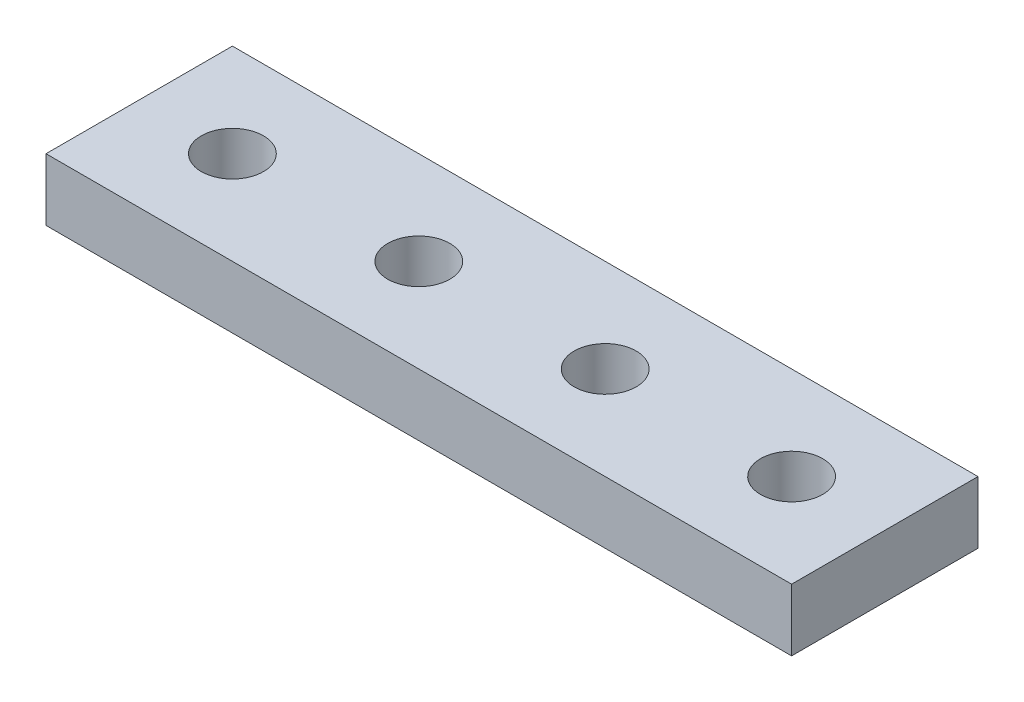
SolidWorks part; units mm, degrees
ref_plane "Front Plane" through (0, 0, 0) normal (0, 0, 1) x (1, 0, 0)
ref_plane "Top Plane" through (0, 0, 0) normal (0, 1, 0) x (1, 0, 0)
ref_plane "Right Plane" through (0, 0, 0) normal (1, 0, 0) x (0, 0, -1)
sketch "Sketch1" plane through (0, 0, 0) normal (0, 1, 0) x (1, 0, 0)
  line L1 (0, 0) -> (120, 0)
  line L2 (0, 0) -> (0, 30)
  line L3 (0, 30) -> (120, 30)
  line L4 (120, 0) -> (120, 30)
  circle A0 centre (15, 15) radius 5
  circle A1 centre (45, 15) radius 5
  circle A2 centre (75, 15) radius 5
  circle A3 centre (105, 15) radius 5
  point P13 (0, 0)
  point P14 (0, 0)
  point P15 (0, 0)
  point P16 (0, 0)
  point P17 (0, 0)
  dimension "D3" = 10
  dimension "D4" = 10
  dimension "D5" = 10
  dimension "D6" = 10
  dimension "D1" = 30
  dimension "D2" = 120
  dimension "D7" = 105
  dimension "D8" = 75
  dimension "D9" = 45
  dimension "D10" = 15
  dimension "D11" = 15
  dimension "D12" = 15
  dimension "D13" = 15
  dimension "D14" = 15
extrude "Boss-Extrude1" add sketch "Sketch1" along normal blind 10
